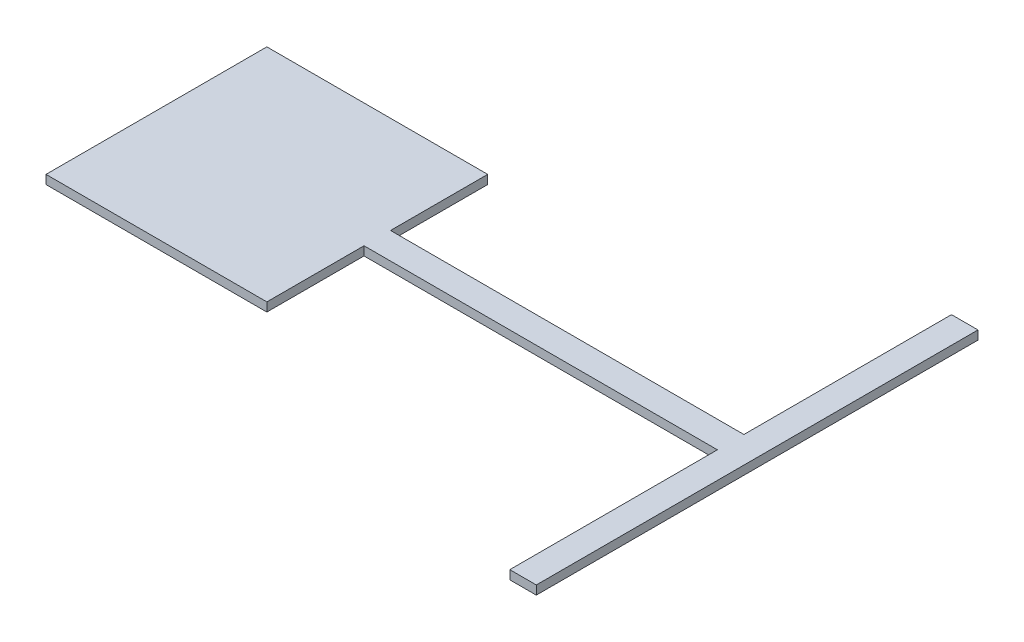
SolidWorks part; units mm, degrees
ref_plane "Front Plane" through (0, 0, 0) normal (0, 0, 1) x (1, 0, 0)
ref_plane "Top Plane" through (0, 0, 0) normal (0, 1, 0) x (1, 0, 0)
ref_plane "Right Plane" through (0, 0, 0) normal (1, 0, 0) x (0, 0, -1)
sketch "Sketch1" plane through (0, 0, 0) normal (0, 1, 0) x (1, 0, 0)
  line L1 (-322.6744, 141.4729) -> (-72.6744, 141.4729)
  line L2 (-322.6744, 141.4729) -> (-322.6744, -108.5271)
  line L3 (-322.6744, -108.5271) -> (-72.6744, -108.5271)
  line L4 (-72.6744, 141.4729) -> (-72.6744, -108.5271)
  line L5 (-72.6744, 1.4729) -> (327.3256, 1.4729)
  line L6 (-72.6744, 1.4729) -> (-72.6744, 31.4729)
  line L7 (-72.6744, 31.4729) -> (327.3256, 31.4729)
  line L8 (327.3256, 1.4729) -> (327.3256, 31.4729)
  line L9 (327.3256, 266.4729) -> (357.3256, 266.4729)
  line L10 (327.3256, 266.4729) -> (327.3256, -233.5271)
  line L11 (327.3256, -233.5271) -> (357.3256, -233.5271)
  line L12 (357.3256, 266.4729) -> (357.3256, -233.5271)
  point P12 (327.3256, 16.4729)
  dimension "D1" = 250
  dimension "D2" = 250
  dimension "D3" = 0
  dimension "D4" = 30
  dimension "D5" = 110
  dimension "D6" = 400
  dimension "D7" = 30
  dimension "D8" = 500
  dimension "D9" = 0
  dimension "D10" = 235
extrude "Boss-Extrude1" add sketch "Sketch1" along normal blind 10 contours L4 L1 L2 L3 | L5 L8 L7 L4 | L12 L9 L10 L8 L11
